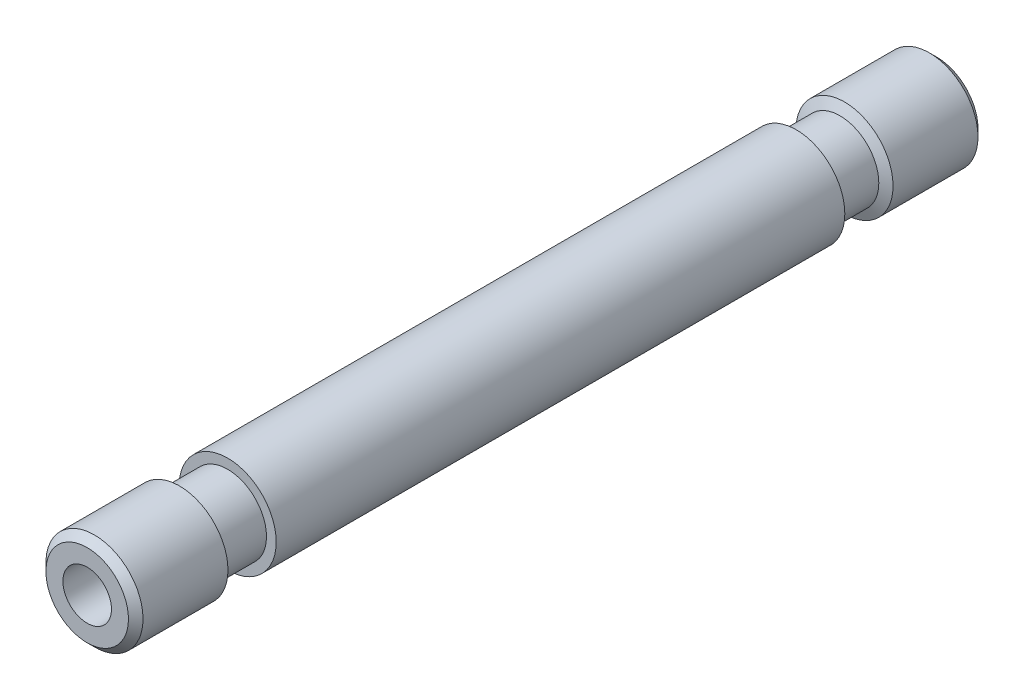
SolidWorks part; units mm, degrees
ref_plane "Front Plane" through (0, 0, 0) normal (0, 0, 1) x (1, 0, 0)
ref_plane "Top Plane" through (0, 0, 0) normal (0, 1, 0) x (1, 0, 0)
ref_plane "Right Plane" through (0, 0, 0) normal (1, 0, 0) x (0, 0, -1)
sketch "Sketch1" plane through (0, 0, 0) normal (1, 0, 0) x (0, 0, -1)
  line L0 (0, 1) -> (35, 1)
  line L1 (35, 1) -> (35, 1.7)
  line L2 (35, 1.7) -> (34.7, 2)
  line L3 (34.7, 2) -> (31.2, 2)
  line L4 (31.2, 2) -> (31.0135, 1.6)
  line L5 (31.0135, 1.6) -> (29.2135, 1.6)
  line L6 (29.2135, 1.6) -> (29.2135, 2)
  line L7 (29.2135, 2) -> (5.7865, 2)
  line L8 (5.7865, 2) -> (5.7865, 1.6)
  line L9 (5.7865, 1.6) -> (3.9865, 1.6)
  line L10 (3.9865, 1.6) -> (3.8, 2)
  line L11 (3.8, 2) -> (0.3, 2)
  line L12 (0.3, 2) -> (0, 1.7)
  line L13 (0, 1.7) -> (0, 1)
  line L14 (35, 0) -> (0, 0) construction
revolve "Revolve1" add sketch "Sketch1" angle 360 about L14
